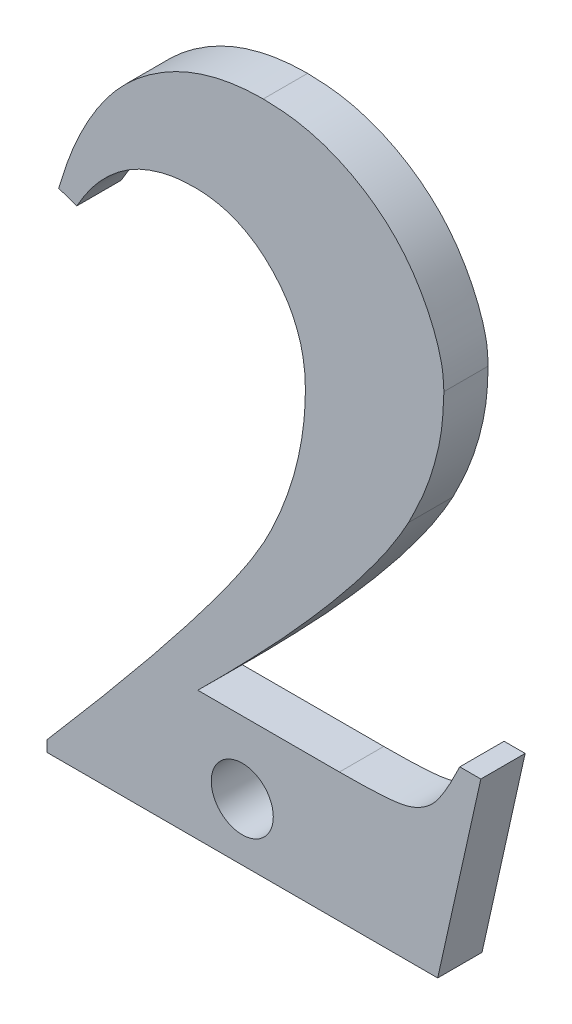
SolidWorks part; units mm, degrees
ref_plane "Plan de face" through (0, 0, 0) normal (0, 0, 1) x (1, 0, 0)
ref_plane "Plan de dessus" through (0, 0, 0) normal (0, 1, 0) x (1, 0, 0)
ref_plane "Plan de droite" through (0, 0, 0) normal (1, 0, 0) x (0, 0, -1)
sketch "Esquisse1" plane through (0, 0, 0) normal (0, 0, 1) x (1, 0, 0)
  text T0 "<b>2</b>\r\n" font "Times New Roman" height 30
extrude "Boss.-Extru.1" add sketch "Esquisse1" along normal blind 2
hole_wizard "Dégagement M1.61" positions "Esquisse2" profile "Esquisse3" hole size "M1.6" standard "Ansi Metric"
sketch "Esquisse2" plane through (0, 0, 2) normal (0, 0, 1) x (1, 0, 0)
  point P8 (21.3607, 13.7923)
  point P11 (18.2988, 7.6336)
  point P12 (21.3607, 13.7923)
sketch "Esquisse3" plane through (21.3607, 13.7923, 2) normal (1, 0, 0) x (0, -1, 0)
  line L0 (0, 0) -> (0, 50)
  line L1 (0, 50) -> (1.4, 50)
  line L2 (1.4, 50) -> (1.4, 0)
  line L5 (1.4, 0) -> (0, 0)
  line L10 (0, 50) -> (-1.4, 50) construction
  line L11 (0, -6.35) -> (0, 107.95) construction
  dimension "Diamètre du perçage" = 2.8
  dimension "Profondeur du perçage" = 50
  dimension "Angle de pointe" = 180
